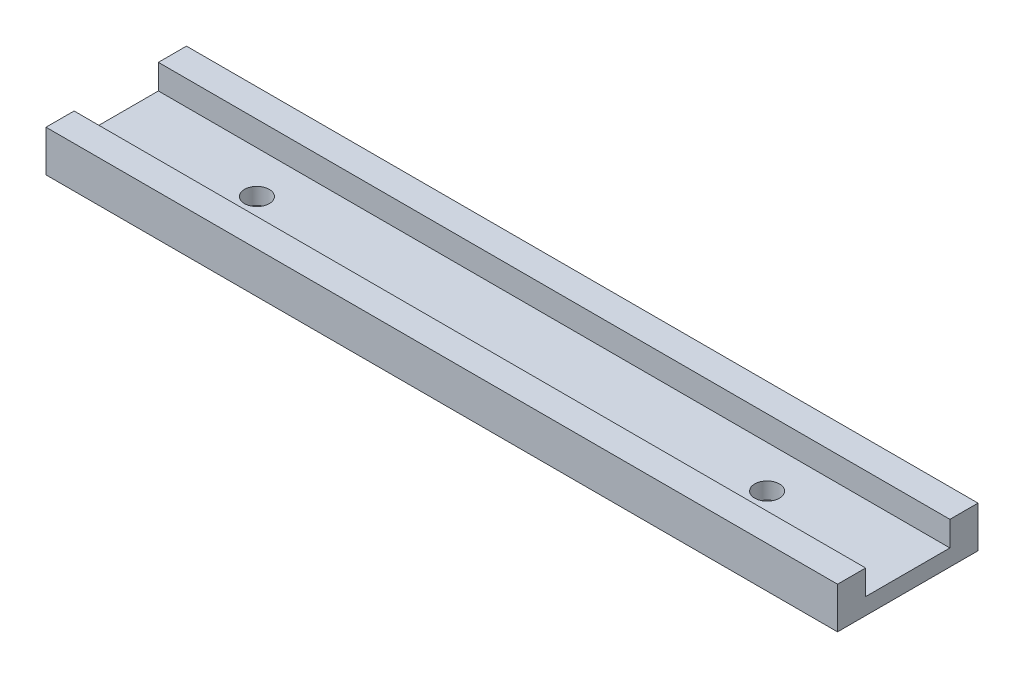
SolidWorks part; units mm, degrees
material "1060 Alloy"
ref_plane "Front Plane" through (0, 0, 0) normal (0, 0, 1) x (1, 0, 0)
ref_plane "Top Plane" through (0, 0, 0) normal (0, 1, 0) x (1, 0, 0)
ref_plane "Right Plane" through (0, 0, 0) normal (1, 0, 0) x (0, 0, -1)
sketch "Sketch1" plane through (0, 0, 0) normal (1, 0, 0) x (0, 0, -1)
  line L0 (-8.5, 0) -> (8.5, 0)
  line L1 (8.5, 0) -> (8.5, 5)
  line L2 (8.5, 5) -> (5.1, 5)
  line L3 (5.1, 5) -> (5.1, 2)
  line L4 (5.1, 2) -> (-5.1, 2)
  line L5 (-5.1, 2) -> (-5.1, 5)
  line L6 (-5.1, 5) -> (-8.5, 5)
  line L7 (-8.5, 5) -> (-8.5, 0)
  point P2 (0, 0)
  point P9 (0, 2)
  dimension "D1" = 17
  dimension "D2" = 10.2
  dimension "D3" = 5
  dimension "D4" = 3
extrude "Boss-Extrude1" add sketch "Sketch1" along normal mid plane 95.8 contours L7 L0 L1 L2 L3 L4 L5 L6
hole_wizard "Ø3.0mm Dowel Hole1" positions "Sketch2" profile "Sketch3" hole size "Ø3.0" standard "ANSI Metric"
sketch "Sketch2" plane through (0, 2, 0) normal (0, 1, 0) x (1, 0, 0)
  line L0 (-30.875, 0) -> (30.875, 0) construction
  point P0 (-30.875, 0)
  point P2 (30.875, 0)
  point P9 (0, 0)
  dimension "D1" = 61.75
sketch "Sketch3" plane through (-30.875, 2, 0) normal (1, 0, 0) x (0, 0, 1)
  line L0 (0, 0) -> (0, 9.4013)
  line L1 (0, 9.4013) -> (1.5, 8.5)
  line L2 (1.5, 8.5) -> (1.5, 0)
  line L5 (1.5, 0) -> (0, 0)
  line L10 (0, 9.4013) -> (-1.5, 8.5) construction
  line L11 (0, -6.35) -> (0, 107.95) construction
  dimension "Hole Dia." = 3
  dimension "Hole Depth" = 8.5
  dimension "Drill Angle" = 118
